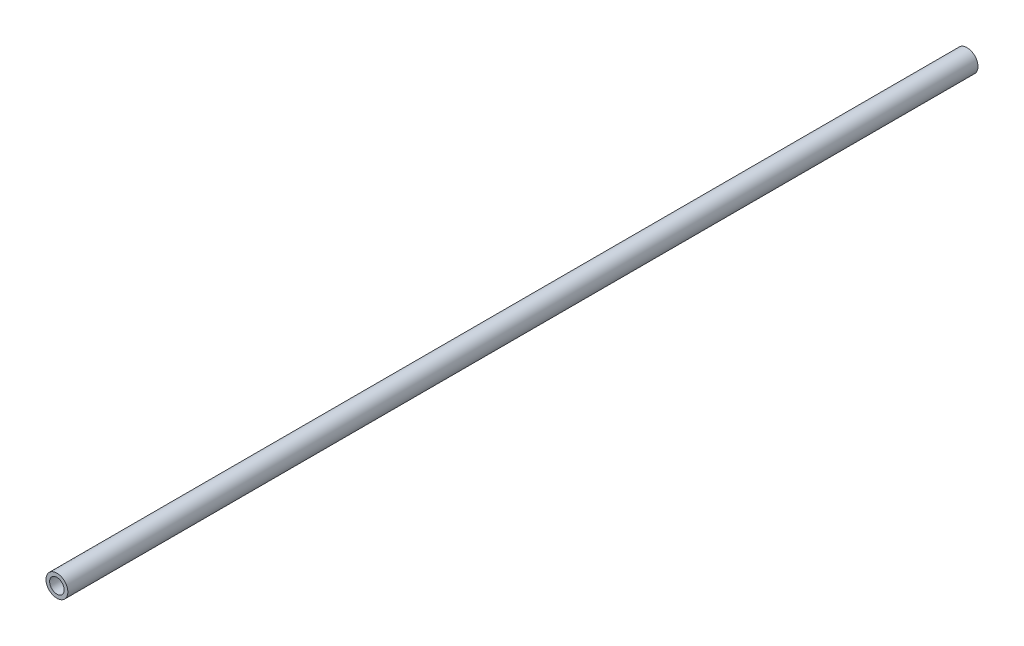
SolidWorks part; units mm, degrees
material "PVC Rigid"
ref_plane "Front Plane" through (0, 0, 0) normal (0, 0, 1) x (1, 0, 0)
ref_plane "Top Plane" through (0, 0, 0) normal (0, 1, 0) x (1, 0, 0)
ref_plane "Right Plane" through (0, 0, 0) normal (1, 0, 0) x (0, 0, -1)
sketch "Sketch1" plane through (0, 0, 0) normal (0, 0, 1) x (1, 0, 0)
  circle A0 centre (0, 0) radius 7.62
  circle A2 centre (0, 0) radius 5.08
  dimension "D1" = 15.24
  dimension "D2" = 10.16
extrude "Boss-Extrude1" add sketch "Sketch1" along normal blind 635
